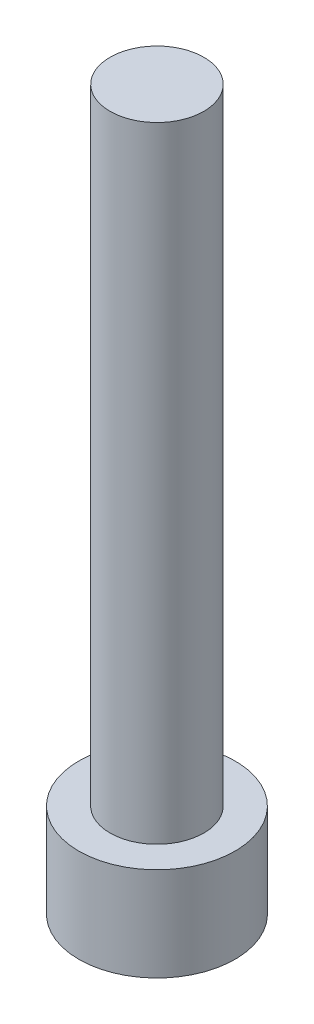
SolidWorks part; units mm, degrees
ref_plane "前视基准面" through (0, 0, 0) normal (0, 0, 1) x (1, 0, 0)
ref_plane "上视基准面" through (0, 0, 0) normal (0, 1, 0) x (1, 0, 0)
ref_plane "右视基准面" through (0, 0, 0) normal (1, 0, 0) x (0, 0, -1)
sketch "草图1" plane through (0, 0, 0) normal (0, 1, 0) x (1, 0, 0)
  circle A0 centre (0, 0) radius 2.5
  dimension "D1" = 5
extrude "凸台-拉伸1" add sketch "草图1" along normal blind 3
sketch "草图2" plane through (0, 3, 0) normal (0, 1, 0) x (1, 0, 0)
  circle A0 centre (0, 0) radius 1.5
extrude "凸台-拉伸2" add sketch "草图2" along normal blind 20
sketch "草图3" plane through (0, 0, 0) normal (0, -1, 0) x (1, 0, 0)
  line L1 (1.425, 0) -> (0.7125, 1.2341)
  line L2 (0.7125, 1.2341) -> (-0.7125, 1.2341)
  line L3 (-0.7125, 1.2341) -> (-1.425, 0)
  line L4 (-1.425, 0) -> (-0.7125, -1.2341)
  line L5 (-0.7125, -1.2341) -> (0.7125, -1.2341)
  line L6 (0.7125, -1.2341) -> (1.425, 0)
  circle A0 centre (0, 0) radius 1.2341 construction
extrude "切除-拉伸1" cut sketch "草图3" against normal blind 1.65
